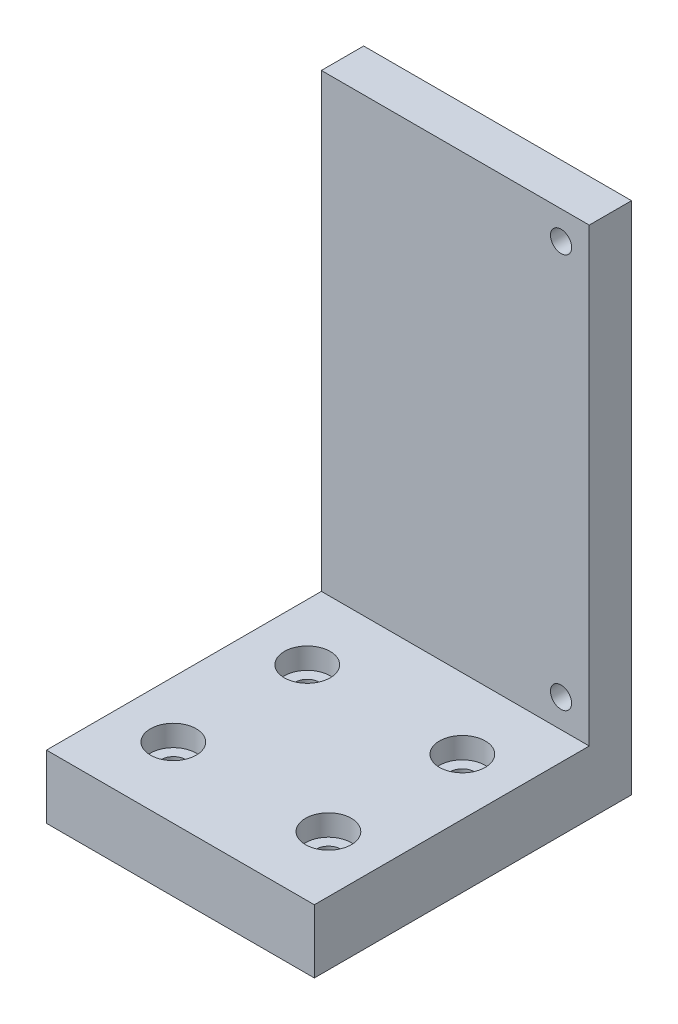
SolidWorks part; units mm, degrees
ref_plane "Front Plane" through (0, 0, 0) normal (0, 0, 1) x (1, 0, 0)
ref_plane "Top Plane" through (0, 0, 0) normal (0, 1, 0) x (1, 0, 0)
ref_plane "Right Plane" through (0, 0, 0) normal (1, 0, 0) x (0, 0, -1)
sketch "Sketch1" plane through (0, 0, 0) normal (0, 1, 0) x (1, 0, 0)
  line L1 (0, 0) -> (38, 0)
  line L2 (0, 0) -> (0, 45)
  line L3 (0, 45) -> (38, 45)
  line L4 (38, 0) -> (38, 45)
  dimension "D1" = 38
  dimension "D2" = 45
extrude "Boss-Extrude2" add sketch "Sketch1" along normal blind 9 contours L3 L4 L1 L2
sketch "Sketch2" plane through (0, 9, 0) normal (0, 1, 0) x (1, 0, 0)
  line L0 (38, 0) -> (38, 45) construction
  line L1 (0, 45) -> (38, 45)
  line L2 (0, 45) -> (0, 39)
  line L3 (0, 39) -> (38, 39)
  line L4 (38, 45) -> (38, 39)
  dimension "D1" = 6
extrude "Boss-Extrude3" add sketch "Sketch2" along normal blind 64
sketch "Sketch3" plane through (0, 0, -39) normal (0, 0, 1) x (1, 0, 0)
  line L0 (38, 73) -> (38, 9) construction
  line L1 (0, 73) -> (38, 73) construction
  line L2 (0, 9) -> (38, 9) construction
  circle A0 centre (34, 69) radius 1.5
  circle A1 centre (34, 13) radius 1.5
  dimension "D1" = 3
  dimension "D2" = 3
  dimension "D4" = 4
  dimension "D5" = 4
  dimension "D6" = 4
  dimension "D3" = 4
extrude "Cut-Extrude1" cut sketch "Sketch3" against normal blind 64
hole_wizard "CBORE for M3 SHCS1" positions "Sketch4" profile "Sketch5" counterbore size "M3" standard "ANSI Metric" end condition through all
sketch "Sketch4" plane through (0, 9, 0) normal (0, 1, 0) x (1, 0, 0)
  line L0 (0, 0) -> (0, 39) construction
  line L1 (38, 0) -> (38, 39) construction
  line L2 (0, 39) -> (38, 39) construction
  line L3 (0, 0) -> (38, 0) construction
  point P0 (8, 29)
  point P2 (8, 10)
  point P4 (30, 10)
  point P6 (30, 29)
  dimension "D1" = 8
  dimension "D2" = 8
  dimension "D3" = 10
  dimension "D4" = 10
sketch "Sketch5" plane through (8, 9, -29) normal (1, 0, 0) x (0, 0, 1)
  line L0 (0, 0) -> (0, 9)
  line L1 (0, 9) -> (1.7, 9)
  line L3 (1.7, 9) -> (1.7, 3)
  line L4 (1.7, 3) -> (3.25, 3)
  line L5 (3.25, 3) -> (3.25, 0)
  line L7 (3.25, 0) -> (0, 0)
  line L11 (0, -6.35) -> (0, 107.95) construction
  dimension "Thru Hole Dia." = 3.4
  dimension "Thru Hole Depth" = 9
  dimension "C'Bore Dia." = 6.5
  dimension "C'Bore Depth" = 3
